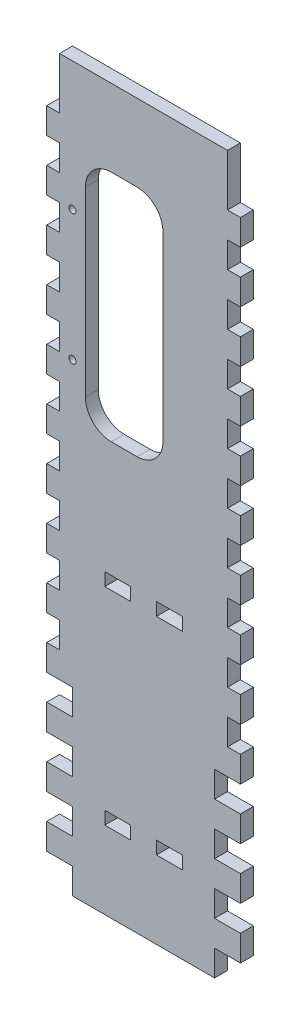
SolidWorks part; units mm, degrees
material "Pine"
ref_plane "Front Plane" through (0, 0, 0) normal (0, 0, 1) x (1, 0, 0)
ref_plane "Top Plane" through (0, 0, 0) normal (0, 1, 0) x (1, 0, 0)
ref_plane "Right Plane" through (0, 0, 0) normal (1, 0, 0) x (0, 0, -1)
sketch "Sketch1" plane through (0, 0, 0) normal (0, 0, 1) x (1, 0, 0)
  line L1 (0, 0) -> (95.25, 0)
  line L2 (0, 0) -> (0, 355.6)
  line L3 (0, 355.6) -> (95.25, 355.6)
  line L4 (95.25, 0) -> (95.25, 355.6)
  dimension "D1" = 95.25
  dimension "D2" = 355.6
extrude "Boss-Extrude1" add sketch "Sketch1" along normal blind 6.35 contours L3 L4 L1 L2
sketch "Sketch2" plane through (0, 0, 6.35) normal (0, 0, 1) x (1, 0, 0)
  line L0 (0, 0) -> (0, 355.6) construction
  line L1 (0, 12.7) -> (12.7, 12.7)
  line L2 (0, 12.7) -> (0, 0)
  line L3 (0, 0) -> (12.7, 0)
  line L4 (12.7, 12.7) -> (12.7, 0)
  line L5 (0, 0) -> (95.25, 0) construction
  line L6 (95.25, 0) -> (95.25, 355.6) construction
  line L7 (95.25, 12.7) -> (82.55, 12.7)
  line L8 (95.25, 12.7) -> (95.25, 0)
  line L9 (95.25, 0) -> (82.55, 0)
  line L10 (82.55, 12.7) -> (82.55, 0)
  dimension "D1" = 12.7
  dimension "D2" = 12.7
extrude "Cut-Extrude1" cut sketch "Sketch2" against normal through all
pattern_linear "LPattern1" count 16 spacing 25.4 along (0, 1, 0) of "Cut-Extrude1"
sketch "Sketch3" plane through (0, 0, 6.35) normal (0, 0, 1) x (1, 0, 0)
  line L0 (47.625, 0) -> (47.625, 41.275) construction
  line L1 (28.575, 44.45) -> (41.275, 44.45)
  line L2 (28.575, 44.45) -> (28.575, 38.1)
  line L3 (28.575, 38.1) -> (41.275, 38.1)
  line L4 (41.275, 44.45) -> (41.275, 38.1)
  line L5 (53.975, 44.45) -> (66.675, 44.45)
  line L6 (53.975, 44.45) -> (53.975, 38.1)
  line L7 (53.975, 38.1) -> (66.675, 38.1)
  line L8 (66.675, 44.45) -> (66.675, 38.1)
  line L9 (12.7, 0) -> (82.55, 0) construction
  line L10 (41.275, 41.275) -> (53.975, 41.275) construction
  dimension "D1" = 12.7
  dimension "D2" = 6.35
  dimension "D3" = 38.1
extrude "Cut-Extrude2" cut sketch "Sketch3" against normal through all
sketch "Sketch4" plane through (0, 0, 6.35) normal (0, 0, 1) x (1, 0, 0)
  line L0 (44.45, 163.25) -> (44.45, 99.25) construction
  line L1 (0, 88.9) -> (0, 101.6) construction
  line L2 (12.7, 0) -> (82.55, 0) construction
  line L4 (44.45, 163.25) -> (57.15, 163.25) construction
  line L5 (44.45, 163.25) -> (44.45, 99.25) construction
  line L6 (44.45, 99.25) -> (57.15, 99.25) construction
  line L7 (57.15, 163.25) -> (57.15, 99.25) construction
  circle A0 centre (44.45, 163.25) radius 1.75
  circle A1 centre (44.45, 99.25) radius 1.75
  circle A2 centre (57.15, 163.25) radius 1.75
  circle A3 centre (57.15, 99.25) radius 1.75
  dimension "D4" = 3.5
  dimension "D1" = 44.45
  dimension "D2" = 64
  dimension "D3" = 99.25
  dimension "D5" = 12.7
pattern_linear "LPattern4" count 2 spacing 76.2 along (0, 1, 0) of "Cut-Extrude2"
sketch "Sketch5" plane through (0, 0, 6.35) normal (0, 0, 1) x (1, 0, 0)
  line L0 (0, 355.6) -> (95.25, 355.6) construction
  line L1 (12.7, 355.6) -> (6.35, 355.6)
  line L2 (12.7, 355.6) -> (12.7, 101.6)
  line L3 (12.7, 101.6) -> (6.35, 101.6)
  line L4 (6.35, 355.6) -> (6.35, 101.6)
  line L5 (0, 101.6) -> (12.7, 101.6) construction
  line L6 (12.7, 101.6) -> (12.7, 114.3) construction
  line L7 (82.55, 101.6) -> (95.25, 101.6) construction
  line L8 (82.55, 355.6) -> (88.9, 355.6)
  line L9 (82.55, 355.6) -> (82.55, 101.6)
  line L10 (82.55, 101.6) -> (88.9, 101.6)
  line L11 (88.9, 355.6) -> (88.9, 101.6)
  line L12 (82.55, 114.3) -> (82.55, 101.6) construction
extrude "Boss-Extrude2" add sketch "Sketch5" against normal through all
sketch "Sketch6" plane through (0, 0, 6.35) normal (0, 0, 1) x (1, 0, 0)
  line L1 (6.35, 342.9) -> (0, 342.9)
  line L2 (6.35, 342.9) -> (6.35, 355.6)
  line L3 (6.35, 355.6) -> (0, 355.6)
  line L4 (0, 342.9) -> (0, 355.6)
  line L5 (88.9, 342.9) -> (95.25, 342.9)
  line L6 (88.9, 342.9) -> (88.9, 355.6)
  line L7 (88.9, 355.6) -> (95.25, 355.6)
  line L8 (95.25, 342.9) -> (95.25, 355.6)
extrude "Cut-Extrude3" cut sketch "Sketch6" against normal through all
sketch "Sketch7" plane through (0, 0, 6.35) normal (0, 0, 1) x (1, 0, 0)
  line L1 (28.575, 120.65) -> (66.675, 120.65)
  line L2 (28.575, 120.65) -> (28.575, 114.3)
  line L3 (28.575, 114.3) -> (66.675, 114.3)
  line L4 (66.675, 120.65) -> (66.675, 114.3)
extrude "Boss-Extrude4" add sketch "Sketch7" against normal through all
sketch "Sketch8" plane through (0, 0, 6.35) normal (0, 0, 1) x (1, 0, 0)
  line L0 (12.7, 0) -> (82.55, 0) construction
  line L1 (28.575, 146.05) -> (41.275, 146.05)
  line L2 (28.575, 146.05) -> (28.575, 139.7)
  line L3 (28.575, 139.7) -> (41.275, 139.7)
  line L4 (41.275, 146.05) -> (41.275, 139.7)
  line L5 (53.975, 146.05) -> (66.675, 146.05)
  line L6 (53.975, 146.05) -> (53.975, 139.7)
  line L7 (53.975, 139.7) -> (66.675, 139.7)
  line L8 (66.675, 146.05) -> (66.675, 139.7)
  line L9 (28.575, 44.45) -> (28.575, 38.1) construction
  line L10 (53.975, 44.45) -> (53.975, 38.1) construction
  line L11 (41.275, 44.45) -> (28.575, 44.45) construction
  dimension "D1" = 146.05
extrude "Cut-Extrude4" cut sketch "Sketch8" against normal through all
sketch "Sketch9" plane through (0, 0, 6.35) normal (0, 0, 1) x (1, 0, 0)
  line L0 (12.7, 292.35) -> (12.7, 228.35) construction
  line L1 (12.7, 0) -> (82.55, 0) construction
  line L2 (6.35, 266.7) -> (6.35, 254) construction
  circle A0 centre (12.7, 292.35) radius 1.75
  circle A1 centre (12.7, 228.35) radius 1.75
  point P2 (12.7, 260.35)
  dimension "D4" = 3.5
  dimension "D1" = 260.35
  dimension "D2" = 64
  dimension "D3" = 6.35
extrude "Cut-Extrude5" cut sketch "Sketch9" against normal through all contours A0 | A1
sketch "Sketch10" plane through (0, 0, 6.35) normal (0, 0, 1) x (1, 0, 0)
  line L0 (6.35, 266.7) -> (6.35, 254) construction
  line L1 (19.05, 317.75) -> (57.15, 317.75)
  line L2 (19.05, 317.75) -> (19.05, 202.95)
  line L3 (19.05, 202.95) -> (57.15, 202.95)
  line L4 (57.15, 317.75) -> (57.15, 202.95)
  circle A0 centre (12.7, 292.35) radius 1.75 construction
  circle A1 centre (12.7, 228.35) radius 1.75 construction
  dimension "D1" = 25.4
  dimension "D2" = 25.4
  dimension "D3" = 12.7
  dimension "D4" = 38.1
extrude "Cut-Extrude6" cut sketch "Sketch10" against normal through all
fillet "Fillet1" radius 12.7 4 edges at (19.05, 202.95, 3.175) (57.15, 202.95, 3.175) (57.15, 317.75, 3.175) (19.05, 317.75, 3.175)
